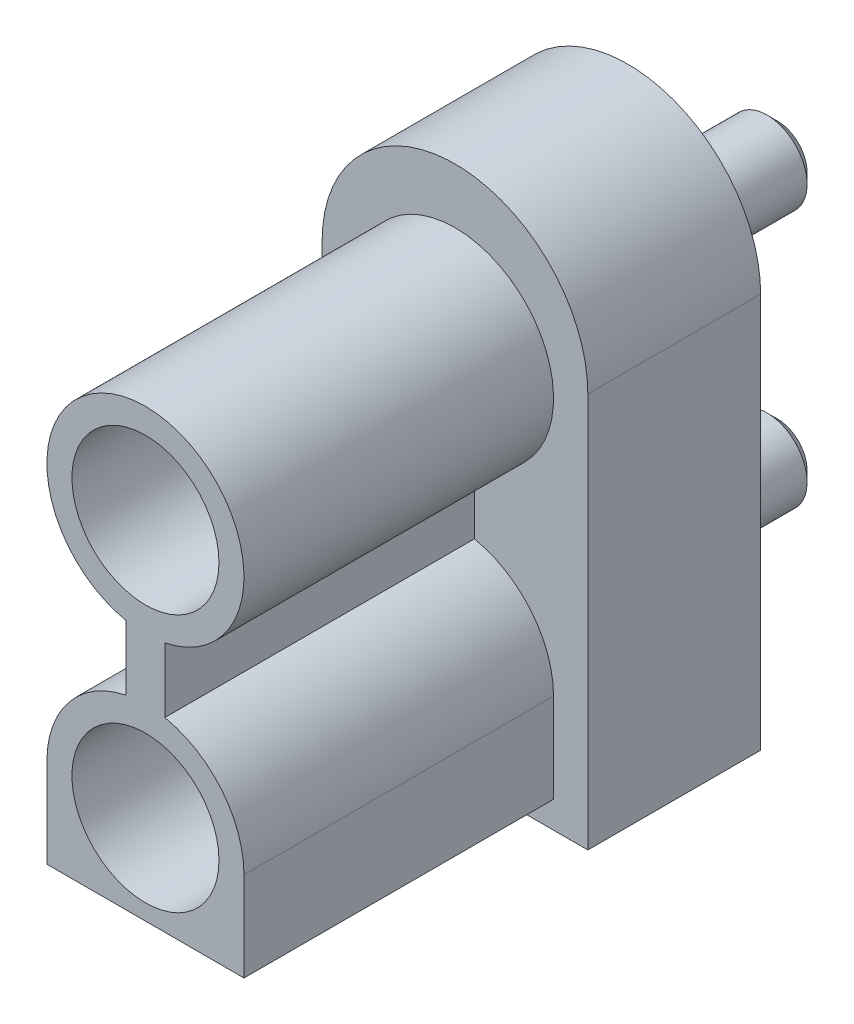
SolidWorks part; units mm, degrees
ref_plane "Alzado" through (0, 0, 0) normal (0, 0, 1) x (1, 0, 0)
ref_plane "Planta" through (0, 0, 0) normal (0, 1, 0) x (1, 0, 0)
ref_plane "Vista lateral" through (0, 0, 0) normal (1, 0, 0) x (0, 0, -1)
sketch "Croquis1" plane through (0, 0, 0) normal (0, 0, 1) x (1, 0, 0)
  line L0 (-2.575, 7.655) -> (-2.575, 0)
  line L1 (-2.575, 0) -> (2.575, 0)
  line L2 (2.575, 0) -> (2.575, 7.655)
  arc A0 (-2.575, 7.655) -> (2.575, 7.655) centre (0, 7.655) cw
  point P4 (0, 0)
  point P7 (0, 10.23)
  dimension "D1" = 5.15
  dimension "D2" = 10.23
extrude "Saliente-Extruir1" add sketch "Croquis1" along normal blind 3.35
sketch "Croquis2" plane through (0, 0, 0) normal (0, 0, -1) x (-1, 0, 0)
  line L0 (2.575, 0) -> (-2.575, 0) construction
  circle A0 centre (0, 7.25) radius 0.775
  circle A1 centre (0, 2.25) radius 0.775
  dimension "D1" = 1.55
  dimension "D2" = 5
  dimension "D3" = 2.25
extrude "Saliente-Extruir2" add sketch "Croquis2" along normal blind 2.9
chamfer "Chaflán1" distance 0.2 angle 45 2 edges at (-0.775, 2.25, -2.9) (-0.775, 7.25, -2.9)
sketch "Croquis3" plane through (0, 0, 3.35) normal (0, 0, 1) x (1, 0, 0)
  line L0 (-1.91, 2.25) -> (-1.91, 0.5186)
  line L1 (-1.91, 0.5186) -> (1.91, 0.5186)
  line L2 (1.91, 0.5186) -> (1.91, 2.25)
  line L3 (0.375, 5.3772) -> (0.375, 4.1228)
  line L4 (-0.375, 5.3772) -> (-0.375, 4.1228)
  line L5 (0, 8.2519) -> (0, 1.7332) construction
  line L6 (-2.575, 0) -> (2.575, 0) construction
  arc A0 (-1.91, 2.25) -> (-0.375, 4.1228) centre (0, 2.25) cw
  circle A1 centre (0, 2.25) radius 1.425
  circle A2 centre (0, 7.25) radius 1.425
  arc A3 (0.375, 5.3772) -> (-0.375, 5.3772) centre (0, 7.25) ccw
  arc A4 (0.375, 4.1228) -> (1.91, 2.25) centre (0, 2.25) cw
  dimension "D1" = 2.85
  dimension "D2" = 3.82
  dimension "D3" = 0.75
  dimension "D4" = 5
  dimension "D5" = 2.25
extrude "Saliente-Extruir3" add sketch "Croquis3" along normal blind 6
